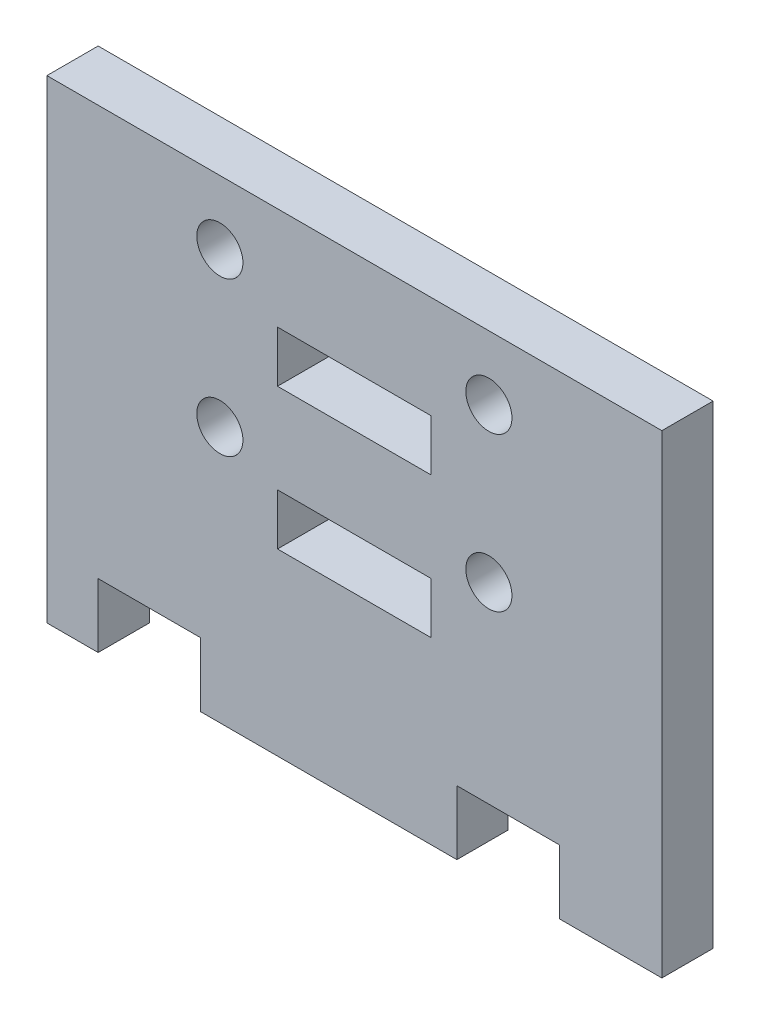
SolidWorks part; units mm, degrees
ref_plane "Front Plane" through (0, 0, 0) normal (0, 0, 1) x (1, 0, 0)
ref_plane "Top Plane" through (0, 0, 0) normal (0, 1, 0) x (1, 0, 0)
ref_plane "Right Plane" through (0, 0, 0) normal (1, 0, 0) x (0, 0, -1)
sketch "Sketch1" plane through (0, 0, 0) normal (0, 0, 1) x (1, 0, 0)
  line L22 (55.2401, 12.5) -> (55.2401, 9) construction
  line L23 (59.2401, 0) -> (49.2401, 0)
  line L24 (59.2401, 0) -> (59.2401, 2.5)
  line L25 (49.2401, 2.5) -> (45.2401, 2.5)
  line L26 (58.2401, 9) -> (58.2401, 7)
  line L27 (52.2401, 9) -> (58.2401, 9)
  line L28 (45.2401, 2.5) -> (45.2401, 0)
  line L29 (58.2401, 7) -> (52.2401, 7)
  line L30 (52.2401, 7) -> (52.2401, 9)
  line L31 (49.2401, 0) -> (49.2401, 2.5)
  line L32 (43.2401, 0) -> (43.2401, 18.5)
  line L33 (45.2401, 0) -> (43.2401, 0)
  line L34 (63.2401, 2.5) -> (63.2401, 0)
  line L35 (52.2401, 12.5) -> (52.2401, 14.5)
  line L36 (58.2401, 12.5) -> (52.2401, 12.5)
  line L37 (52.2401, 14.5) -> (58.2401, 14.5)
  line L38 (58.2401, 14.5) -> (58.2401, 12.5)
  line L39 (67.2401, 0) -> (67.2401, 18.5)
  line L40 (67.2401, 18.5) -> (43.2401, 18.5)
  line L41 (63.2401, 0) -> (67.2401, 0)
  line L42 (63.2401, 2.5) -> (59.2401, 2.5)
  circle A4 centre (60.4901, 10) radius 0.9
  circle A5 centre (49.9901, 16) radius 0.9
  circle A6 centre (49.9901, 10) radius 0.9
  circle A7 centre (60.4901, 16) radius 0.9
  dimension "D2" = 18.5
  dimension "D3" = 2
  dimension "D4" = 4
  dimension "D5" = 16
  dimension "D1" = 1.8
  dimension "D14" = 24
  dimension "D6" = 2.5
  dimension "D7" = 4
  dimension "D8" = 2
  dimension "D9" = 6
  dimension "D10" = 2.5
  dimension "D11" = 2.5
  dimension "D12" = 4.5
  dimension "D13" = 10.5
extrude "Boss-Extrude1" add sketch "Sketch1" along normal blind 2
equation "\"D13@Sketch1\"= \"fingerWidth@parametersSketch@prostheticParameters.SLDPRT\" - 5.7'Hole distance"
equation "\"D1@Sketch1\"= 1.5 + \"tol1@parametersSketch@prostheticParameters.SLDPRT\""
